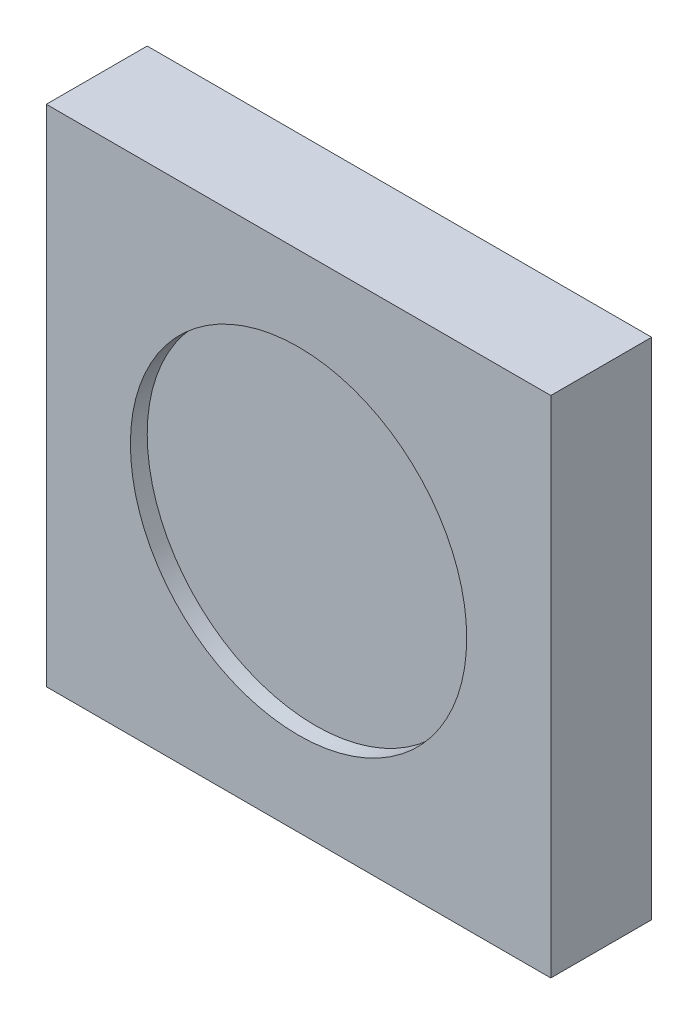
SolidWorks part; units mm, degrees
ref_plane "前视基准面" through (0, 0, 0) normal (0, 0, 1) x (1, 0, 0)
ref_plane "上视基准面" through (0, 0, 0) normal (0, 1, 0) x (1, 0, 0)
ref_plane "右视基准面" through (0, 0, 0) normal (1, 0, 0) x (0, 0, -1)
other "Configuration Table"
sketch "草图1" plane through (0, 0, 0) normal (0, 0, 1) x (1, 0, 0)
  line L1 (-169.2128, 34.7546) -> (-139.2128, 34.7546)
  line L2 (-169.2128, 34.7546) -> (-169.2128, 4.7546)
  line L3 (-169.2128, 4.7546) -> (-139.2128, 4.7546)
  line L4 (-139.2128, 34.7546) -> (-139.2128, 4.7546)
  dimension "D1" = 30
  dimension "D2" = 30
extrude "凸台-拉伸1" add sketch "草图1" along normal blind 6
sketch "草图2" plane through (0, 0, 6) normal (0, 0, 1) x (1, 0, 0)
  circle A0 centre (-154.2128, 19.7546) radius 10
  dimension "D1" = 20
extrude "切除-拉伸1" cut sketch "草图2" against normal blind 1
